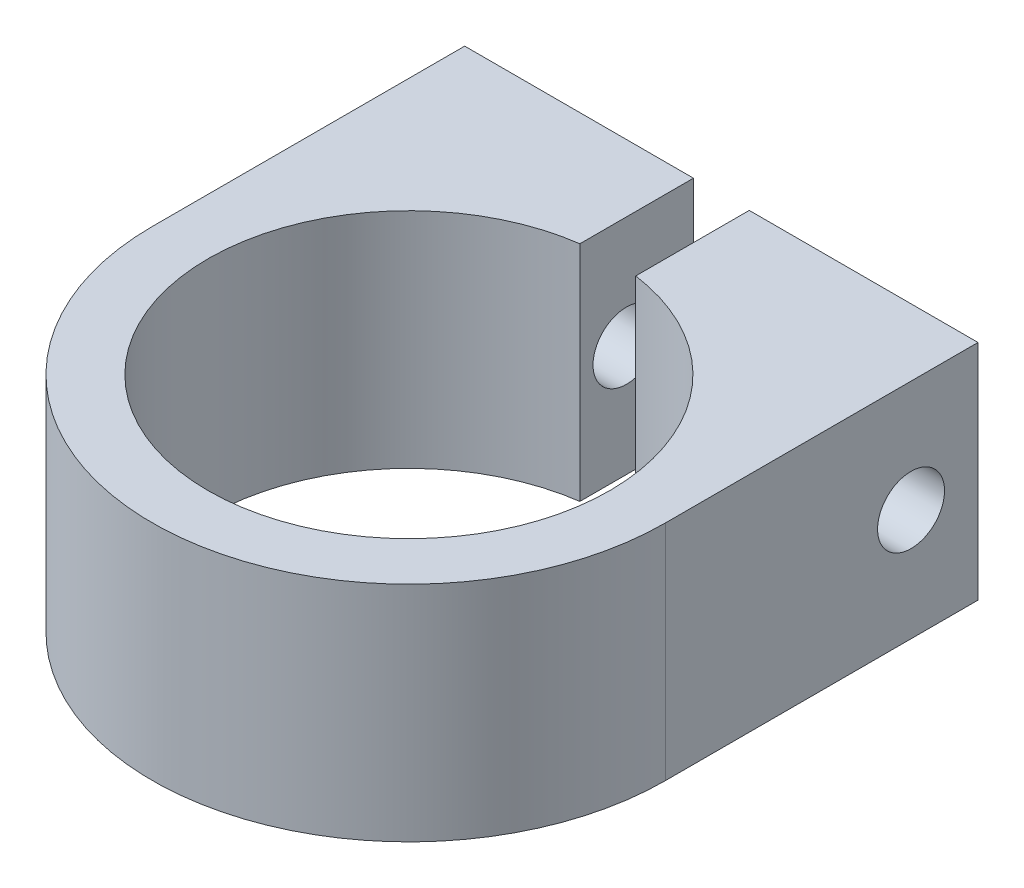
SolidWorks part; units mm, degrees
ref_plane "Plan de face" through (0, 0, 0) normal (0, 0, 1) x (1, 0, 0)
ref_plane "Plan de dessus" through (0, 0, 0) normal (0, 1, 0) x (1, 0, 0)
ref_plane "Plan de droite" through (0, 0, 0) normal (1, 0, 0) x (0, 0, -1)
sketch "Esquisse1" plane through (0, 0, 0) normal (0, 1, 0) x (1, 0, 0)
  line L0 (-23, 0) -> (-23, 28)
  line L1 (-23, 28) -> (-2.5, 28)
  line L2 (23, 0) -> (23, 28)
  line L3 (23, 28) -> (2.5, 28)
  line L4 (2.5, 28) -> (2.5, 17.8255)
  line L5 (-2.5, 28) -> (-2.5, 17.8255)
  arc A0 (-23, 0) -> (23, 0) centre (0, 0) ccw
  arc A1 (-2.5, 17.8255) -> (2.5, 17.8255) centre (0, 0) ccw
  dimension "D1" = 18
  dimension "D2" = 23
  dimension "D3" = 5
  dimension "D4" = 28
  dimension "D5" = 20.5
extrude "Boss.-Extru.1" add sketch "Esquisse1" along normal blind 20
sketch "Esquisse2" plane through (23, 0, 0) normal (1, 0, 0) x (0, 0, -1)
  line L0 (28, 20) -> (28, 0) construction
  line L1 (0, 20) -> (28, 20) construction
  circle A0 centre (22, 10) radius 3
  dimension "D1" = 6
  dimension "D2" = 6
  dimension "D3" = 10
extrude "Enlèv. mat.-Extru.1" cut sketch "Esquisse2" against normal through all
sketch "Esquisse3" plane through (-23, 0, 0) normal (-1, 0, 0) x (0, 0, 1)
  line L0 (-28, 20) -> (-28, 0) construction
  line L1 (-22, 4.2265) -> (-17, 7.1132)
  line L2 (-17, 7.1132) -> (-17, 12.8868)
  line L3 (-17, 12.8868) -> (-22, 15.7735)
  line L4 (-22, 15.7735) -> (-27, 12.8868)
  line L5 (-27, 12.8868) -> (-27, 7.1132)
  line L6 (-27, 7.1132) -> (-22, 4.2265)
  line L7 (-28, 0) -> (0, 0) construction
  circle A0 centre (-22, 10) radius 5 construction
  point P1 (-28, 10)
  dimension "D1" = 10
  dimension "D2" = 6
  dimension "D3" = 10
extrude "Enlèv. mat.-Extru.2" cut sketch "Esquisse3" against normal blind 10
